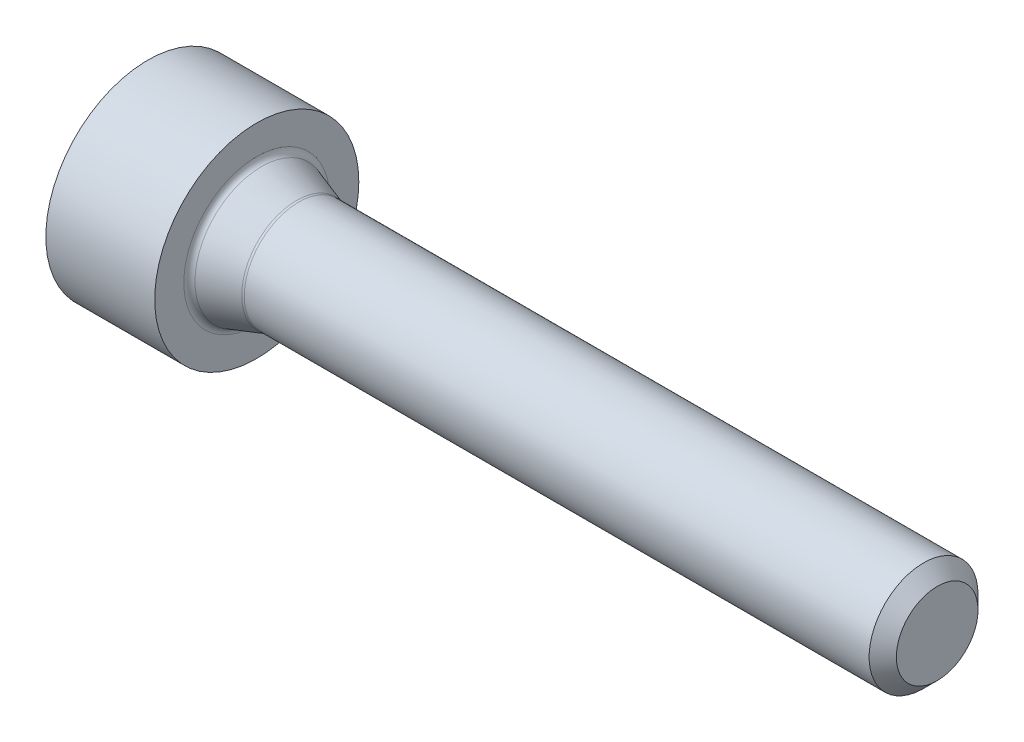
SolidWorks part; units mm, degrees
material "AISI 1020"
ref_plane "Спереди" through (0, 0, 0) normal (0, 0, 1) x (1, 0, 0)
ref_plane "Сверху" through (0, 0, 0) normal (0, 1, 0) x (1, 0, 0)
ref_plane "Справа" through (0, 0, 0) normal (1, 0, 0) x (0, 0, -1)
sketch "Эскиз1" plane through (0, 0, 0) normal (0, 0, 1) x (1, 0, 0)
  line L0 (0, 0) -> (-49757.948, 0) construction
  line L1 (0, 0) -> (0, 1.5)
  line L2 (0, 1.5) -> (1.6, 1.5)
  line L3 (1.6, 1.5) -> (1.6, 1)
  line L4 (1.6, 1) -> (2.2, 0.8)
  line L5 (2.2, 0.8) -> (11.6, 0.8)
  line L6 (11.6, 0.8) -> (11.6, 0)
  line L7 (0, 0) -> (11.6, 0)
  dimension "D1" = 1.6
  dimension "D2" = 10
  dimension "D3" = 1.6
  dimension "D4" = 2
  dimension "D5" = 0.6
  dimension "D6" = 3
revolve "Повернуть1" add sketch "Эскиз1" angle 360 about L0
fillet "Скругление1" radius 0.1 2 edges at (2.2, 0, -0.8) (1.6, 0, -1)
chamfer "Фаска1" distance 0.2 angle 45 1 edges at (11.6, 0, -0.8)
sketch "Эскиз2" plane through (0, 0, 0) normal (-1, 0, 0) x (0, 0, 1)
  line L1 (0, 0.8665) -> (-0.7504, 0.4333)
  line L2 (-0.7504, 0.4333) -> (-0.7504, -0.4333)
  line L3 (-0.7504, -0.4333) -> (0, -0.8665)
  line L4 (0, -0.8665) -> (0.7504, -0.4333)
  line L5 (0.7504, -0.4333) -> (0.7504, 0.4333)
  line L6 (0.7504, 0.4333) -> (0, 0.8665)
  circle A0 centre (0, 0) radius 0.8665 construction
  dimension "D1" = 1.733
extrude "Вырез-Вытянуть1" cut sketch "Эскиз2" against normal blind 0.7
